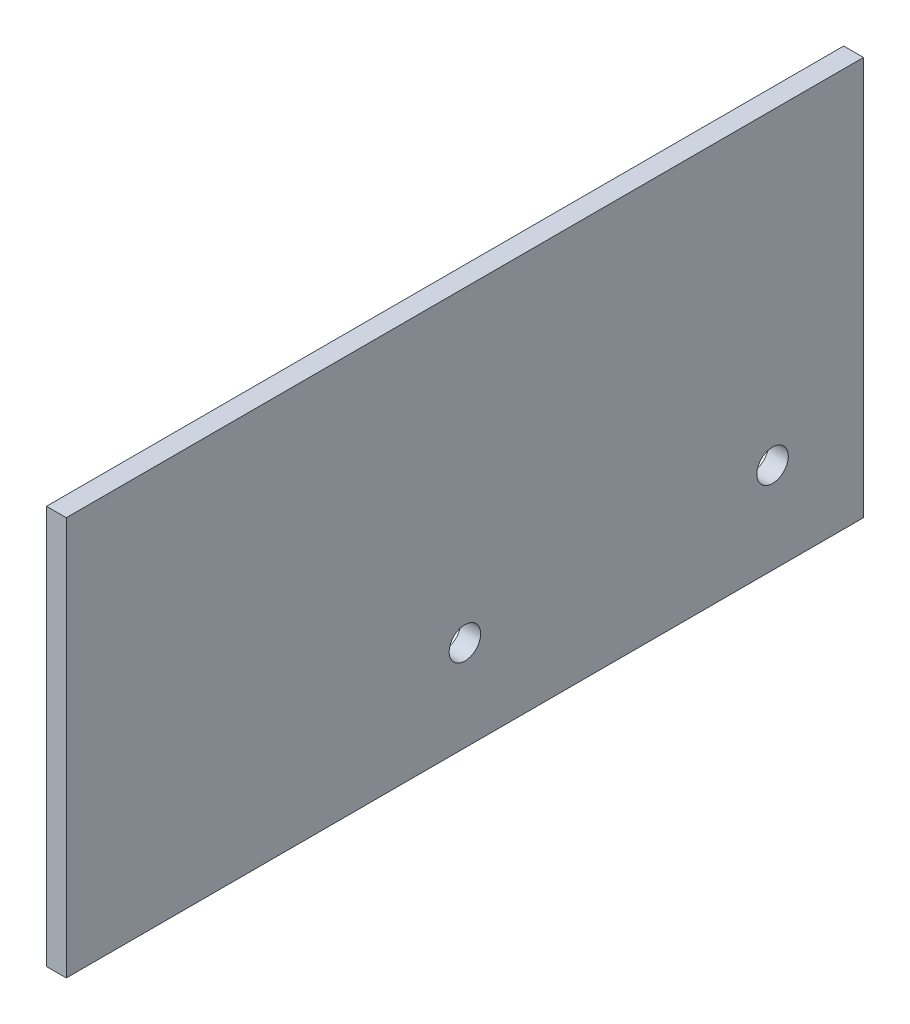
SolidWorks part; units mm, degrees
material "Black Acrylic"
ref_plane "Front Plane" through (0, 0, 0) normal (0, 0, 1) x (1, 0, 0)
ref_plane "Top Plane" through (0, 0, 0) normal (0, 1, 0) x (1, 0, 0)
ref_plane "Right Plane" through (0, 0, 0) normal (1, 0, 0) x (0, 0, -1)
sketch "Sketch1" plane through (0, 0, 0) normal (1, 0, 0) x (0, 0, -1)
  line L0 (-90.5, 0) -> (-90.5, -90.5)
  line L1 (-90.5, -90.5) -> (90.5, -90.5)
  line L2 (90.5, -90.5) -> (90.5, 0)
  line L3 (90.5, 0) -> (-90.5, 0)
  line L4 (90.5, -90.5) -> (-90.5, 90.5) construction
  line L5 (-90.5, -90.5) -> (90.5, 90.5) construction
  line L6 (90.5, -90.5) -> (90.5, 90.5) construction
  point P4 (0, 0)
  dimension "D1" = 181
  dimension "D2" = 181
extrude "Boss-Extrude1" add sketch "Sketch1" along normal mid plane 4.5
extrude "Cut-Extrude1" cut sketch "Sketch2" against normal through all both and the other way through all
sketch "Sketch2" plane through (-88.25, 0, 0) normal (1, 0, 0) x (0, 0, -1)
  line L0 (0, -69.85) -> (0, 69.85) construction
  line L1 (0, 69.85) -> (-69.85, 69.85) construction
  line L2 (69.85, -69.85) -> (0, -69.85) construction
  circle A0 centre (0, -69.85) radius 3.5687
  circle A1 centre (-69.85, 69.85) radius 3.5687
  circle A2 centre (69.85, -69.85) radius 3.5687
  circle A3 centre (0, 69.85) radius 3.5687
